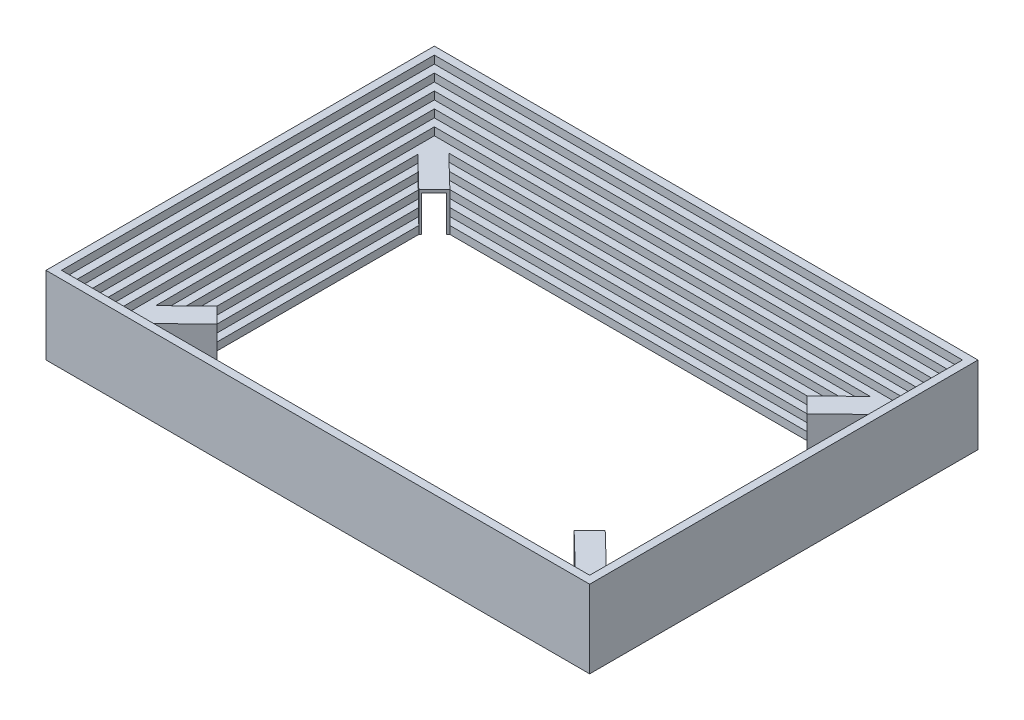
SolidWorks part; units mm, degrees
ref_plane "Plan de face" through (0, 0, 0) normal (0, 0, 1) x (1, 0, 0)
ref_plane "Plan de dessus" through (0, 0, 0) normal (0, 1, 0) x (1, 0, 0)
ref_plane "Plan de droite" through (0, 0, 0) normal (1, 0, 0) x (0, 0, -1)
sketch "Esquisse1" plane through (0, 0, 0) normal (0, 1, 0) x (1, 0, 0)
  line L0 (17500, 12500) -> (17500, -12500)
  line L1 (-12500, 7500) -> (12500, 7500)
  line L2 (-12500, 7500) -> (-12500, -7500)
  line L3 (-12500, -7500) -> (12500, -7500)
  line L4 (12500, 7500) -> (12500, -7500)
  line L5 (-12500, 7500) -> (12500, -7500) construction
  line L6 (-12500, -7500) -> (12500, 7500) construction
  line L7 (-17500, -12500) -> (17500, -12500)
  line L8 (-17500, 12500) -> (-17500, -12500)
  line L9 (-17500, 12500) -> (17500, 12500)
  point P0 (0, 0)
  dimension "D1" = 25000
  dimension "D2" = 15000
  dimension "D3" = 5000
extrude "Boss.-Extru.2" add sketch "Esquisse1" along normal blind 5000
sketch "Esquisse2" plane through (0, 5000, 0) normal (0, 1, 0) x (1, 0, 0)
  line L0 (17500, -12500) -> (17500, 12500) construction
  line L1 (-17000, 12000) -> (17000, 12000)
  line L2 (-17000, 12000) -> (-17000, -12000)
  line L3 (-17000, -12000) -> (17000, -12000)
  line L4 (17000, 12000) -> (17000, -12000)
  line L5 (-17000, 12000) -> (17000, -12000) construction
  line L6 (-17000, -12000) -> (17000, 12000) construction
  line L7 (-17500, -12500) -> (17500, -12500) construction
  point P0 (0, 0)
  dimension "D1" = 500
  dimension "D2" = 500
extrude "Enlèv. mat.-Extru.1" cut sketch "Esquisse2" against normal blind 500
sketch "Esquisse3" plane through (0, 4500, 0) normal (0, 1, 0) x (1, 0, 0)
  line L0 (17000, -12000) -> (17000, 12000) construction
  line L1 (-16500, 11500) -> (16500, 11500)
  line L2 (-16500, 11500) -> (-16500, -11500)
  line L3 (-16500, -11500) -> (16500, -11500)
  line L4 (16500, 11500) -> (16500, -11500)
  line L5 (-16500, 11500) -> (16500, -11500) construction
  line L6 (-16500, -11500) -> (16500, 11500) construction
  line L7 (-17000, -12000) -> (17000, -12000) construction
  point P0 (0, 0)
  dimension "D1" = 500
  dimension "D2" = 500
extrude "Enlèv. mat.-Extru.2" cut sketch "Esquisse3" against normal blind 500
sketch "Esquisse4" plane through (0, 4000, 0) normal (0, 1, 0) x (1, 0, 0)
  line L1 (-16000, 11000) -> (16000, 11000)
  line L2 (-16000, 11000) -> (-16000, -11000)
  line L3 (-16000, -11000) -> (16000, -11000)
  line L4 (16000, 11000) -> (16000, -11000)
  line L5 (-16000, 11000) -> (16000, -11000) construction
  line L6 (-16000, -11000) -> (16000, 11000) construction
  line L7 (16500, -11500) -> (16500, 11500) construction
  line L8 (-16500, -11500) -> (16500, -11500) construction
  point P0 (0, 0)
  dimension "D1" = 500
  dimension "D2" = 500
extrude "Enlèv. mat.-Extru.3" cut sketch "Esquisse4" against normal blind 500
sketch "Esquisse5" plane through (0, 3500, 0) normal (0, 1, 0) x (1, 0, 0)
  line L0 (16000, -11000) -> (16000, 11000) construction
  line L1 (-15500, 10500) -> (15500, 10500)
  line L2 (-15500, 10500) -> (-15500, -10500)
  line L3 (-15500, -10500) -> (15500, -10500)
  line L4 (15500, 10500) -> (15500, -10500)
  line L5 (-15500, 10500) -> (15500, -10500) construction
  line L6 (-15500, -10500) -> (15500, 10500) construction
  line L7 (-16000, -11000) -> (16000, -11000) construction
  point P0 (0, 0)
  dimension "D1" = 500
  dimension "D2" = 500
extrude "Enlèv. mat.-Extru.4" cut sketch "Esquisse5" against normal blind 500
sketch "Esquisse6" plane through (0, 3000, 0) normal (0, 1, 0) x (1, 0, 0)
  line L0 (15500, 10500) -> (-15500, 10500) construction
  line L1 (-15000, -10000) -> (15000, -10000)
  line L2 (-15000, -10000) -> (-15000, 10000)
  line L3 (-15000, 10000) -> (15000, 10000)
  line L4 (15000, -10000) -> (15000, 10000)
  line L5 (-15000, -10000) -> (15000, 10000) construction
  line L6 (-15000, 10000) -> (15000, -10000) construction
  line L7 (15500, -10500) -> (15500, 10500) construction
  point P0 (0, 0)
  dimension "D1" = 500
  dimension "D2" = 500
extrude "Enlèv. mat.-Extru.5" cut sketch "Esquisse6" against normal blind 500
sketch "Esquisse7" plane through (0, 2500, 0) normal (0, 1, 0) x (1, 0, 0)
  line L0 (15000, -10000) -> (15000, 10000) construction
  line L1 (-14500, 9500) -> (14500, 9500)
  line L2 (-14500, 9500) -> (-14500, -9500)
  line L3 (-14500, -9500) -> (14500, -9500)
  line L4 (14500, 9500) -> (14500, -9500)
  line L5 (-14500, 9500) -> (14500, -9500) construction
  line L6 (-14500, -9500) -> (14500, 9500) construction
  line L7 (-15000, -10000) -> (15000, -10000) construction
  point P0 (0, 0)
  dimension "D1" = 500
  dimension "D2" = 500
extrude "Enlèv. mat.-Extru.6" cut sketch "Esquisse7" against normal blind 500
sketch "Esquisse8" plane through (0, 2000, 0) normal (0, 1, 0) x (1, 0, 0)
  line L0 (14500, -9500) -> (14500, 9500) construction
  line L1 (-14000, 9000) -> (14000, 9000)
  line L2 (-14000, 9000) -> (-14000, -9000)
  line L3 (-14000, -9000) -> (14000, -9000)
  line L4 (14000, 9000) -> (14000, -9000)
  line L5 (-14000, 9000) -> (14000, -9000) construction
  line L6 (-14000, -9000) -> (14000, 9000) construction
  line L7 (14500, 9500) -> (-14500, 9500) construction
  point P0 (0, 0)
  dimension "D1" = 500
  dimension "D2" = 500
extrude "Enlèv. mat.-Extru.7" cut sketch "Esquisse8" against normal blind 500
sketch "Esquisse9" plane through (0, 1500, 0) normal (0, 1, 0) x (1, 0, 0)
  line L0 (14000, -9000) -> (14000, 9000) construction
  line L1 (-13500, 8500) -> (13500, 8500)
  line L2 (-13500, 8500) -> (-13500, -8500)
  line L3 (-13500, -8500) -> (13500, -8500)
  line L4 (13500, 8500) -> (13500, -8500)
  line L5 (-13500, 8500) -> (13500, -8500) construction
  line L6 (-13500, -8500) -> (13500, 8500) construction
  line L7 (-14000, -9000) -> (14000, -9000) construction
  point P0 (0, 0)
  dimension "D1" = 500
  dimension "D2" = 500
extrude "Enlèv. mat.-Extru.8" cut sketch "Esquisse9" against normal blind 500
sketch "Esquisse10" plane through (0, 1000, 0) normal (0, 1, 0) x (1, 0, 0)
  line L0 (13500, -8500) -> (13500, 8500) construction
  line L1 (-13000, 8000) -> (13000, 8000)
  line L2 (-13000, 8000) -> (-13000, -8000)
  line L3 (-13000, -8000) -> (13000, -8000)
  line L4 (13000, 8000) -> (13000, -8000)
  line L5 (-13000, 8000) -> (13000, -8000) construction
  line L6 (-13000, -8000) -> (13000, 8000) construction
  line L7 (-13500, -8500) -> (13500, -8500) construction
  point P0 (0, 0)
  dimension "D1" = 500
  dimension "D2" = 500
extrude "Enlèv. mat.-Extru.9" cut sketch "Esquisse10" against normal blind 500
sketch "Esquisse11" plane through (0, 2500, 0) normal (0, 1, 0) x (1, 0, 0)
  line L0 (-12500, -7500) -> (-12500, -6500) construction
  line L1 (-12500, -6500) -> (-17000, -10850.6851)
  line L2 (-12500, 7500) -> (-12500, -7500) construction
  line L3 (-12500, -7500) -> (-11500, -7500) construction
  line L4 (-12500, -7500) -> (12500, -7500) construction
  line L5 (-12500, -6500) -> (-6649.1306, -843.2688) construction
  line L6 (-17000, 12000) -> (-17000, -12000) construction
  line L7 (-11500, -7500) -> (-16154.4394, -12000)
  line L8 (-17000, -12000) -> (17000, -12000) construction
  line L9 (-12500, -6500) -> (-11500, -7500)
  line L10 (-17000, -10850.6851) -> (-16154.4394, -12000)
  line L11 (0, 0) -> (8140.3836, 0) construction
  line L12 (8140.3836, 0) -> (0, 0) construction
  line L13 (0, 0) -> (0, 3723.2534) construction
  line L14 (-12500, 7500) -> (-11500, 7500) construction
  line L15 (-12500, 7500) -> (-12500, 6500) construction
  line L16 (-17000, 10850.6851) -> (-16154.4394, 12000)
  line L17 (-12500, 6500) -> (-11500, 7500)
  line L18 (-11500, 7500) -> (-16154.4394, 12000)
  line L19 (-12500, 6500) -> (-17000, 10850.6851)
  line L20 (12500, 7500) -> (12500, 6500) construction
  line L21 (12500, 7500) -> (11500, 7500) construction
  line L22 (12500, -6500) -> (6649.1306, -843.2688) construction
  line L23 (12500, -7500) -> (11500, -7500) construction
  line L24 (12500, -7500) -> (12500, -6500) construction
  line L25 (12500, 6500) -> (17000, 10850.6851)
  line L26 (11500, 7500) -> (16154.4394, 12000)
  line L27 (12500, 6500) -> (11500, 7500)
  line L28 (17000, 10850.6851) -> (16154.4394, 12000)
  line L29 (17000, -10850.6851) -> (16154.4394, -12000)
  line L30 (12500, -6500) -> (11500, -7500)
  line L31 (11500, -7500) -> (16154.4394, -12000)
  line L32 (12500, -6500) -> (17000, -10850.6851)
  dimension "D1" = 1000
extrude "Boss.-Extru.4" add sketch "Esquisse11" against normal up to surface (2500 mm away) up to face at (0, 0, 0)
sketch "Esquisse12" plane through (9500, 0, -9500) normal (-0.7071, 0, 0.7071) x (0.7071, 0, 0.7071)
  line L0 (2828.4271, 0) -> (4242.6407, 0) construction
  line L1 (3018.8861, 0) -> (4031.5816, 0)
  line L2 (3018.8861, 0) -> (3018.8861, 2272.3851)
  line L3 (3018.8861, 2272.3851) -> (4031.5816, 2272.3851)
  line L4 (4031.5816, 0) -> (4031.5816, 2272.3851)
  line L5 (4242.6407, 500) -> (4242.6407, 2500) construction
  point P8 (4242.6407, 1500)
  dimension "D1" = 211.059
extrude "Enlèv. mat.-Extru.10" cut sketch "Esquisse12" against normal blind 5000
sketch "Esquisse13" plane through (9500, 0, 9500) normal (-0.7071, 0, -0.7071) x (-0.7071, 0, 0.7071)
  line L0 (-4242.6407, 0) -> (-2828.4271, 0) construction
  line L1 (-4104.0507, 0) -> (-2983.47, 0)
  line L2 (-4104.0507, 0) -> (-4104.0507, 2341.1672)
  line L3 (-4104.0507, 2341.1672) -> (-2983.47, 2341.1672)
  line L4 (-2983.47, 0) -> (-2983.47, 2341.1672)
  point P6 (-4104.0507, 0)
extrude "Enlèv. mat.-Extru.11" cut sketch "Esquisse13" against normal blind 5000
sketch "Esquisse14" plane through (-9500, 0, 9500) normal (0.7071, 0, -0.7071) x (-0.7071, 0, -0.7071)
  line L0 (2828.4271, 0) -> (4242.6407, 0) construction
  line L1 (2934.3836, 0) -> (4129.0773, 0)
  line L2 (2934.3836, 0) -> (2934.3836, 2270.0465)
  line L3 (2934.3836, 2270.0465) -> (4129.0773, 2270.0465)
  line L4 (4129.0773, 0) -> (4129.0773, 2270.0465)
extrude "Enlèv. mat.-Extru.12" cut sketch "Esquisse14" against normal blind 5000
sketch "Esquisse15" plane through (-9500, 0, -9500) normal (0.7071, 0, 0.7071) x (0.7071, 0, -0.7071)
  line L0 (-4242.6407, 0) -> (-2828.4271, 0) construction
  line L1 (-4127.9587, 0) -> (-2972.1246, 0)
  line L2 (-4127.9587, 0) -> (-4127.9587, 2314.5921)
  line L3 (-4127.9587, 2314.5921) -> (-2972.1246, 2314.5921)
  line L4 (-2972.1246, 0) -> (-2972.1246, 2314.5921)
extrude "Enlèv. mat.-Extru.14" cut sketch "Esquisse15" against normal blind 5000
